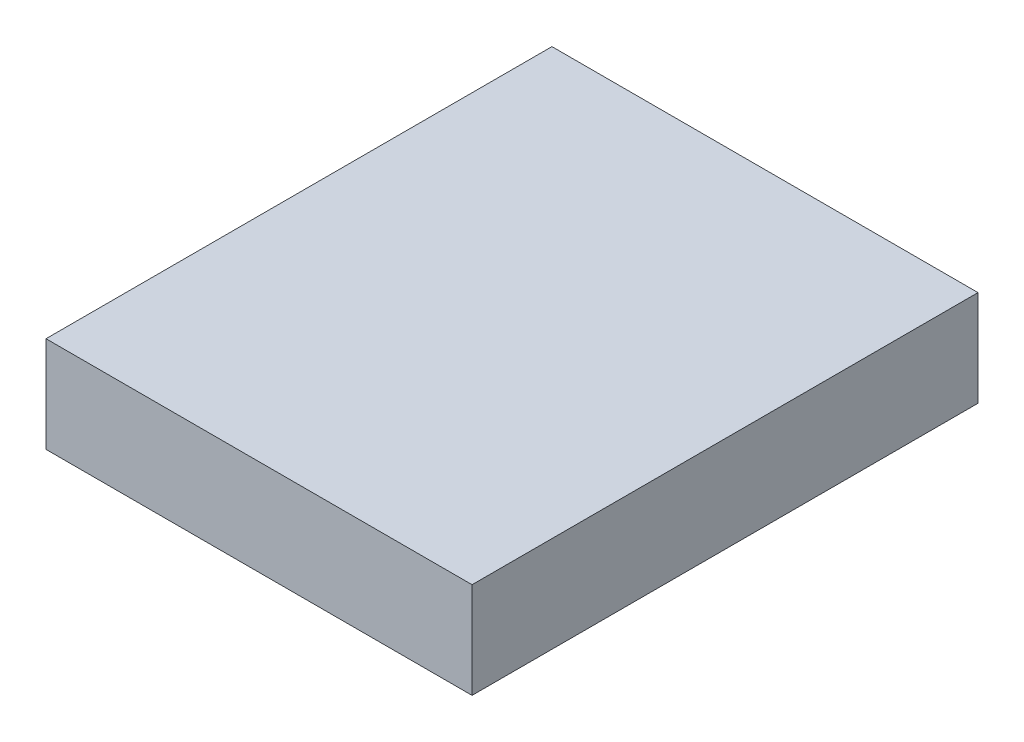
SolidWorks part; units mm, degrees
material "Pin"
ref_plane "Plan de face" through (0, 0, 0) normal (0, 0, 1) x (1, 0, 0)
ref_plane "Plan de dessus" through (0, 0, 0) normal (0, 1, 0) x (1, 0, 0)
ref_plane "Plan de droite" through (0, 0, 0) normal (1, 0, 0) x (0, 0, -1)
sketch "Esquisse1" plane through (0, 0, 0) normal (0, 1, 0) x (1, 0, 0)
  line L1 (-81.7486, 51.1966) -> (-1.7486, 51.1966)
  line L2 (-81.7486, 51.1966) -> (-81.7486, -43.8034)
  line L3 (-81.7486, -43.8034) -> (-1.7486, -43.8034)
  line L4 (-1.7486, 51.1966) -> (-1.7486, -43.8034)
  dimension "D1" = 95
  dimension "D2" = 80
extrude "Boss.-Extru.1" add sketch "Esquisse1" along normal blind 18
